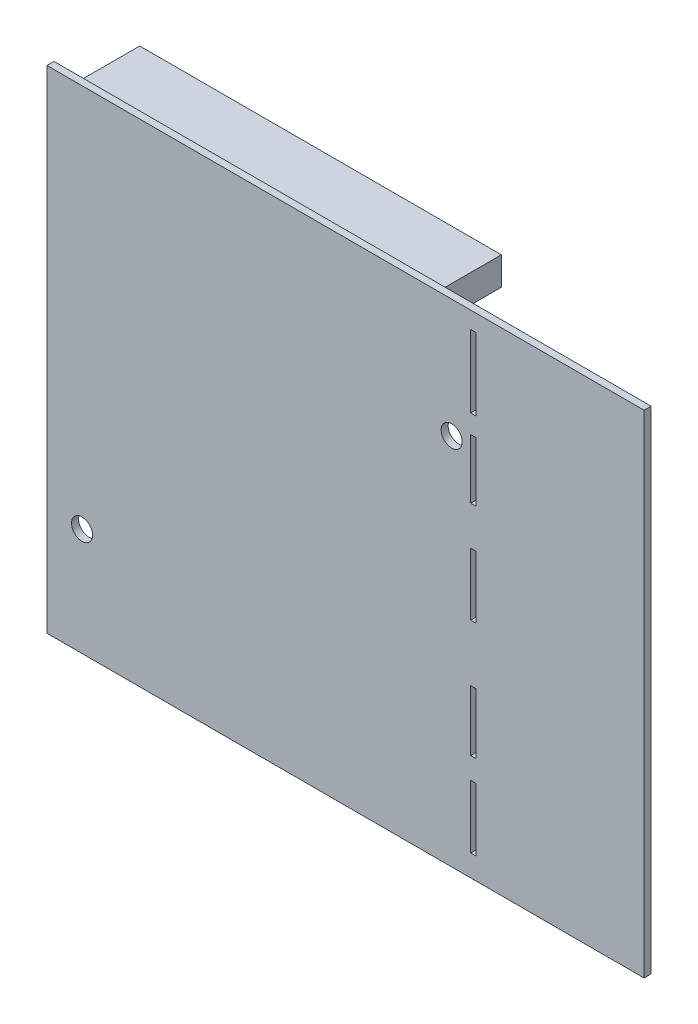
SolidWorks part; units mm, degrees
ref_plane "Alzado" through (0, 0, 0) normal (0, 0, 1) x (1, 0, 0)
ref_plane "Planta" through (0, 0, 0) normal (0, 1, 0) x (1, 0, 0)
ref_plane "Vista lateral" through (0, 0, 0) normal (1, 0, 0) x (0, 0, -1)
sketch "Sketch1" plane through (0, 0, 0) normal (0, 0, 1) x (1, 0, 0)
  line L1 (-51.6522, 41.3997) -> (33.3478, 41.3997)
  line L2 (-51.6522, 41.3997) -> (-51.6522, -28.6003)
  line L3 (-51.6522, -28.6003) -> (33.3478, -28.6003)
  line L4 (33.3478, 41.3997) -> (33.3478, -28.6003)
  dimension "D1" = 85
  dimension "D2" = 70
extrude "Boss-Extrude1" add sketch "Sketch1" along normal blind 1
sketch "Sketch2" plane through (0, 0, 0) normal (0, 0, -1) x (-1, 0, 0)
  line L0 (51.6522, -28.6003) -> (-33.3478, -28.6003) construction
  line L1 (49.4478, 39.3997) -> (-2.0355, 39.3997)
  line L2 (49.4478, 39.3997) -> (49.4478, 35.3997)
  line L3 (49.4478, 35.3997) -> (-2.0355, 35.3997)
  line L4 (-2.0355, 39.3997) -> (-2.0355, 35.3997)
  line L5 (-2.0355, -26.6003) -> (49.4478, -26.6003)
  line L6 (-2.0355, -26.6003) -> (-2.0355, -22.6003)
  line L7 (-2.0355, -22.6003) -> (49.4478, -22.6003)
  line L8 (49.4478, -26.6003) -> (49.4478, -22.6003)
  line L9 (-33.3478, 41.3997) -> (51.6522, 41.3997) construction
  dimension "D1" = 4
  dimension "D2" = 4
  dimension "D3" = 2
  dimension "D4" = 2
extrude "Boss-Extrude2" add sketch "Sketch2" along normal blind 10 separate body
sketch "Sketch3" plane through (0, 0, 0) normal (0, 0, -1) x (-1, 0, 0)
  line L1 (-9.461, 39.0223) -> (-8.6689, 39.0223)
  line L2 (-9.461, 39.0223) -> (-9.461, 28.7256)
  line L3 (-9.461, 28.7256) -> (-8.6689, 28.7256)
  line L4 (-8.6689, 39.0223) -> (-8.6689, 28.7256)
  line L5 (-9.461, 26.0598) -> (-8.6689, 26.0598)
  line L6 (-9.461, 26.0598) -> (-9.461, 17.597)
  line L7 (-9.461, 17.597) -> (-8.6689, 17.597)
  line L8 (-8.6689, 26.0598) -> (-8.6689, 17.597)
  line L9 (-9.461, 12.0417) -> (-8.6689, 12.0417)
  line L10 (-9.461, 12.0417) -> (-9.461, 3.1726)
  line L11 (-9.461, 3.1726) -> (-8.6689, 3.1726)
  line L12 (-8.6689, 12.0417) -> (-8.6689, 3.1726)
  line L13 (-9.461, -4.9012) -> (-8.6689, -4.9012)
  line L14 (-9.461, -4.9012) -> (-9.461, -13.514)
  line L15 (-9.461, -13.514) -> (-8.6689, -13.514)
  line L16 (-8.6689, -4.9012) -> (-8.6689, -13.514)
  line L17 (-9.461, -16.5704) -> (-8.6689, -16.5704)
  line L18 (-9.461, -16.5704) -> (-9.461, -25.526)
  line L19 (-9.461, -25.526) -> (-8.6689, -25.526)
  line L20 (-8.6689, -16.5704) -> (-8.6689, -25.526)
extrude "Cut-Extrude1" cut sketch "Sketch3" against normal blind 10
sketch "Sketch4" plane through (0, 0, -10) normal (0, 0, -1) x (-1, 0, 0)
  line L0 (51.6522, 41.3997) -> (51.6522, -28.6003) construction
  circle A0 centre (46.6522, -13.2697) radius 1.5
  circle A1 centre (-5.9624, 24.5376) radius 1.5
  dimension "D1" = 3
  dimension "D2" = 5
extrude "Cut-Extrude3" cut sketch "Sketch4" against normal blind 33
